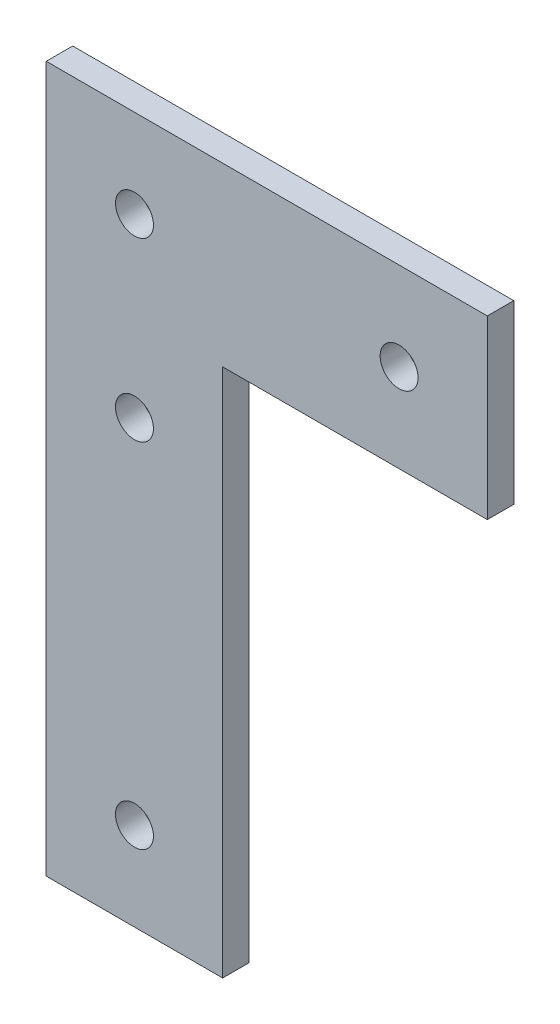
SolidWorks part; units mm, degrees
material "Thornel Mat VMA"
ref_plane "Front Plane" through (0, 0, 0) normal (0, 0, 1) x (1, 0, 0)
ref_plane "Top Plane" through (0, 0, 0) normal (0, 1, 0) x (1, 0, 0)
ref_plane "Right Plane" through (0, 0, 0) normal (1, 0, 0) x (0, 0, -1)
sketch "Sketch1" plane through (0, 0, 0) normal (0, 0, 1) x (1, 0, 0)
  line L0 (-350.6121, 147.905) -> (329.3879, 147.905) construction
  line L1 (-300.6121, 147.905) -> (-350.6121, 147.905)
  line L2 (-300.6121, 147.905) -> (-300.6121, 127.905)
  line L3 (-300.6121, 127.905) -> (-330.6121, 127.905)
  line L4 (-350.6121, 147.905) -> (-350.6121, 127.905)
  line L5 (-350.6121, -492.095) -> (-350.6121, -382.095) construction
  line L6 (-350.6121, 67.905) -> (-350.6121, 147.905) construction
  line L7 (-350.6121, 67.905) -> (-330.6121, 67.905)
  line L8 (-350.6121, 67.905) -> (-350.6121, 127.905)
  line L10 (-330.6121, 67.905) -> (-330.6121, 127.905)
  line L11 (-330.6121, 67.905) -> (-350.6121, 67.905) construction
  line L12 (-300.6121, 147.905) -> (-300.6121, 127.905) construction
  line L13 (-350.6121, 147.905) -> (-300.6121, 147.905) construction
  circle A0 centre (-340.6121, 77.905) radius 2.15 construction
  circle A1 centre (-340.6121, 117.905) radius 2.15 construction
  circle A2 centre (-340.6121, 137.905) radius 2.15 construction
  circle A3 centre (-310.6121, 137.905) radius 2.15 construction
  circle A4 centre (-340.6121, 77.905) radius 2.15
  circle A5 centre (-340.6121, 117.905) radius 2.15
  circle A6 centre (-340.6121, 137.905) radius 2.15
  circle A7 centre (-310.6121, 137.905) radius 2.15
extrude "Extrude1" add sketch "Sketch1" along normal blind 3
